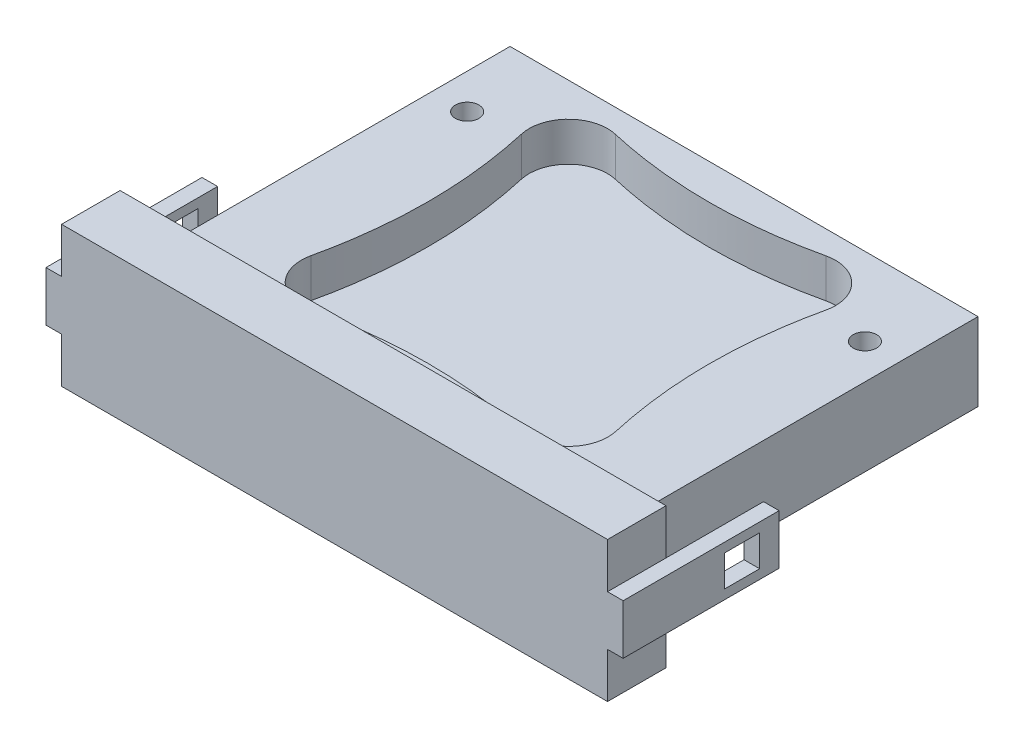
SolidWorks part; units mm, degrees
ref_plane "Front Plane" through (0, 0, 0) normal (0, 0, 1) x (1, 0, 0)
ref_plane "Top Plane" through (0, 0, 0) normal (0, 1, 0) x (1, 0, 0)
ref_plane "Right Plane" through (0, 0, 0) normal (1, 0, 0) x (0, 0, -1)
sketch "Sketch1" plane through (0, 0, 0) normal (0, 1, 0) x (1, 0, 0)
  line L1 (-30, -22.5) -> (30, -22.5)
  line L2 (-30, -22.5) -> (-30, 22.5)
  line L3 (-30, 22.5) -> (30, 22.5)
  line L4 (30, -22.5) -> (30, 22.5)
  line L5 (-30, -22.5) -> (30, 22.5) construction
  line L6 (-30, 22.5) -> (30, -22.5) construction
  point P0 (0, 0)
  dimension "D1" = 45
  dimension "D2" = 60
extrude "Boss-Extrude1" add sketch "Sketch1" along normal blind 10
sketch "Sketch2" plane through (0, 0, 22.5) normal (0, 0, 1) x (1, 0, 0)
  line L0 (0, 0) -> (0, 10) construction
  line L1 (-30, 10) -> (30, 10) construction
  line L2 (-30, 5) -> (30, 5) construction
  line L3 (-30, 10) -> (-30, 0) construction
  line L4 (30, 10) -> (30, 0) construction
  line L6 (-35, -4) -> (35, -4)
  line L7 (-35, -4) -> (-35, 14)
  line L8 (-35, 14) -> (35, 14)
  line L9 (35, -4) -> (35, 14)
  line L10 (-35, -4) -> (35, 14) construction
  line L11 (-35, 14) -> (35, -4) construction
  point P11 (0, 5)
  dimension "D1" = 5
  dimension "D2" = 4
extrude "Boss-Extrude2" add sketch "Sketch2" along normal blind 7.5
sketch "Sketch3" plane through (0, 10, 0) normal (0, 1, 0) x (1, 0, 0)
  line L0 (-18.0125, 0) -> (18.0125, 0) construction
  line L1 (0, -17.955) -> (0, 17.955) construction
  line L3 (-19.5325, -13.495) -> (19.5325, -13.495) construction
  line L4 (-19.5325, -13.495) -> (-19.5325, 13.495) construction
  line L5 (-19.5325, 13.495) -> (19.5325, 13.495) construction
  line L6 (19.5325, -13.495) -> (19.5325, 13.495) construction
  line L7 (-19.5325, -13.495) -> (19.5325, 13.495) construction
  line L8 (-19.5325, 13.495) -> (19.5325, -13.495) construction
  line L9 (-13.49, 19.495) -> (13.49, 19.495) construction
  line L10 (-13.49, 19.495) -> (-13.49, -19.495) construction
  line L11 (-13.49, -19.495) -> (13.49, -19.495) construction
  line L12 (13.49, 19.495) -> (13.49, -19.495) construction
  line L13 (-13.49, 19.495) -> (13.49, -19.495) construction
  line L14 (-13.49, -19.495) -> (13.49, 19.495) construction
  arc A0 (-19.5325, -13.495) -> (-13.49, -19.495) centre (-14.6292, -14.5996) ccw
  arc A1 (-19.5325, 13.495) -> (-13.49, 19.495) centre (-14.6292, 14.5996) cw
  arc A2 (13.49, 19.495) -> (19.5325, 13.495) centre (14.6117, 14.582) cw
  arc A3 (13.49, -19.495) -> (19.5325, -13.495) centre (14.6117, -14.582) ccw
  spline S0 degree 2 poles (19.5325, 13.495) (16.4925, 0) (19.5325, -13.495) knots 0 0 0 1 1 1
  spline S1 degree 3 poles (-19.5325, 13.495) (-18.5192, 8.9967) (-17.5058, 0) (-18.5192, -8.9967) (-19.5325, -13.495) knots 0 0 0 0 0.5 1 1 1 1
  spline S2 degree 3 poles (-13.49, 19.495) (-4.4967, 17.4417) (4.4967, 17.4417) (13.49, 19.495) knots 0 0 0 0 1 1 1 1
  spline S3 degree 3 poles (-13.49, -19.495) (-4.4967, -17.4417) (4.4967, -17.4417) (13.49, -19.495) knots 0 0 0 0 1 1 1 1
  point P0 (0, 0)
  point P3 (0, 0)
  point P4 (0, 0)
  point P8 (0, 0)
  dimension "D7" = 5.0262
  dimension "D8" = 5.0262
  dimension "D9" = 5.0394
  dimension "D10" = 5.0394
  dimension "D1" = 36.025
  dimension "D2" = 35.91
  dimension "D3" = 26.99
  dimension "D4" = 39.065
  dimension "D5" = 38.99
  dimension "D6" = 26.98
extrude "Cut-Extrude1" cut sketch "Sketch3" against normal blind 5
sketch "Sketch4" plane through (35, 0, 0) normal (1, 0, 0) x (0, 0, -1)
  line L0 (-30, 5) -> (-30, 8.2)
  line L1 (-30, -4) -> (-30, 14) construction
  line L2 (-30, 8.2) -> (-10, 8.2)
  line L3 (-10, 8.2) -> (-10, 1.8)
  line L4 (-10, 1.8) -> (-30, 1.8)
  line L5 (-30, 1.8) -> (-30, 5)
  line L6 (-30, 5) -> (-12.5, 5) construction
  line L8 (-17, 3) -> (-12.5, 3)
  line L9 (-17, 3) -> (-17, 7)
  line L10 (-17, 7) -> (-12.5, 7)
  line L11 (-12.5, 3) -> (-12.5, 7)
  line L12 (-17, 3) -> (-12.5, 7) construction
  line L13 (-17, 7) -> (-12.5, 3) construction
  point P4 (-14.75, 5)
  dimension "D1" = 3.2
  dimension "D2" = 3.2
  dimension "D3" = 20
  dimension "D4" = 2.5
  dimension "D5" = 4.5
  dimension "D6" = 4
extrude "Boss-Extrude3" add sketch "Sketch4" along normal blind 2
mirror "Mirror1" about plane through (0, 0, 0) normal (1, 0, 0) of "Boss-Extrude3"
sketch "Sketch5" plane through (0, 10, 0) normal (0, 1, 0) x (1, 0, 0)
  line L0 (30, -22.5) -> (30, 22.5) construction
  line L2 (-30, -22.5) -> (30, -22.5) construction
  circle A0 centre (25.5, 12.5) radius 1.5
  dimension "D3" = 3
  dimension "D1" = 4.5
  dimension "D2" = 35
extrude "Cut-Extrude2" cut sketch "Sketch5" against normal through all
mirror "Mirror2" about plane through (0, 0, 0) normal (1, 0, 0) of "Cut-Extrude2"
